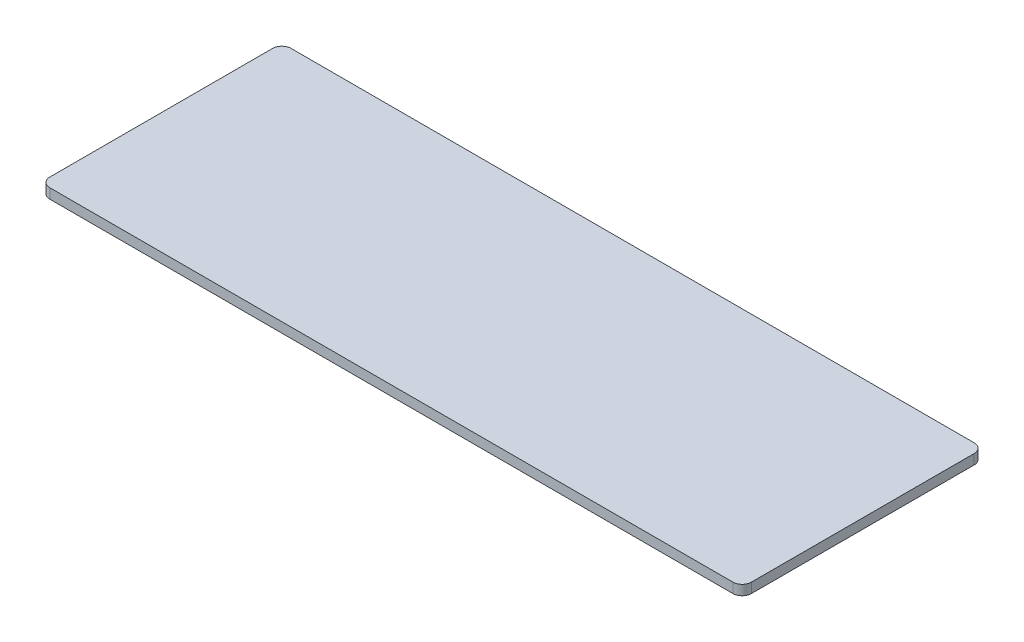
SolidWorks part; units mm, degrees
ref_plane "Front Plane" through (0, 0, 0) normal (0, 0, 1) x (1, 0, 0)
ref_plane "Top Plane" through (0, 0, 0) normal (0, 1, 0) x (1, 0, 0)
ref_plane "Right Plane" through (0, 0, 0) normal (1, 0, 0) x (0, 0, -1)
sketch "Sketch2" plane through (0, 0, 0) normal (0, 1, 0) x (1, 0, 0)
  line L1 (37.8, 13) -> (-37.8, 13)
  line L2 (37.8, 13) -> (37.8, -13)
  line L3 (37.8, -13) -> (-37.8, -13)
  line L4 (-37.8, 13) -> (-37.8, -13)
  line L5 (37.8, 13) -> (-37.8, -13) construction
  line L6 (37.8, -13) -> (-37.8, 13) construction
  point P0 (0, 0)
  dimension "D1" = 75.6
  dimension "D2" = 26
extrude "Boss-Extrude1" add sketch "Sketch2" along normal mid plane 1.07
fillet "Fillet1" radius 1 4 edges at (-37.8, 0, 13) (-37.8, 0, -13) (37.8, 0, -13) (37.8, 0, 13)
equation "\"∩╗┐cas_w\" = 38.1mm"
equation "\"cas_l\" = 83.0mm"
equation "\"cas_h\" = 280.0mm"
equation "\"rail_w\" = 50.5mm"
equation "\"rail_c\" = 10.5mm"
equation "\"stinset_l\" = 160mm"
equation "\"stinset_w\" = 110mm"
equation "\"stinset_h\" = 3mm"
equation "\"stinset_fillet\" = 5mm"
equation "\"slide_l\" = 75.6mm"
equation "\"slide_w\" = 26mm"
equation "\"slide_h\" = 1.07mm"
equation "\"slide_fillet\" = 1mm"
equation "\"D1@Sketch2\"=\"slide_l\""
equation "\"D2@Sketch2\"=\"slide_w\""
equation "\"D1@Boss-Extrude1\"=\"slide_h\""
